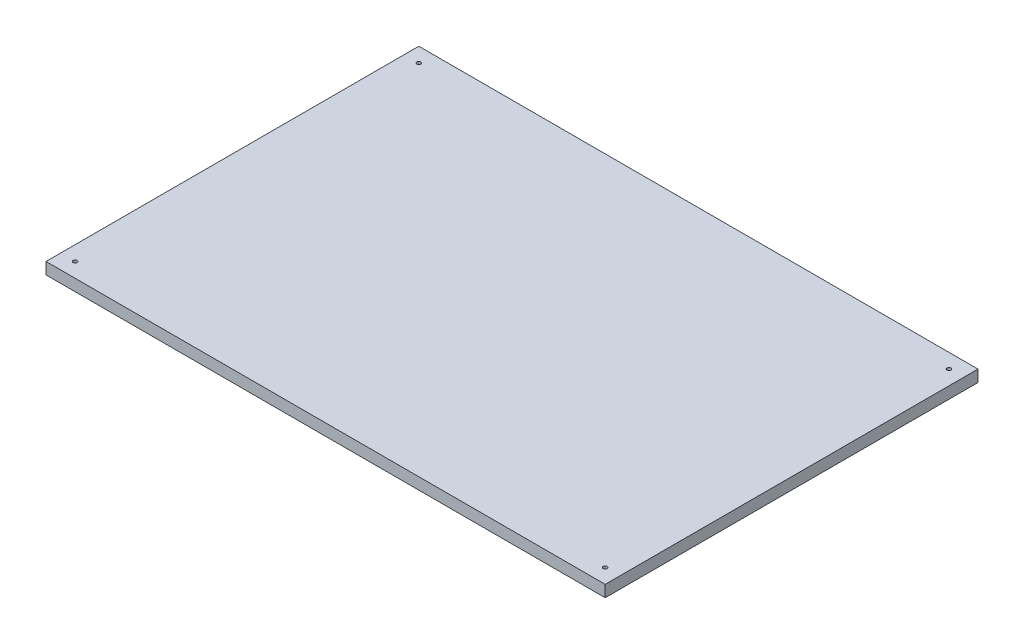
SolidWorks part; units mm, degrees
ref_plane "Front Plane" through (0, 0, 0) normal (0, 0, 1) x (1, 0, 0)
ref_plane "Top Plane" through (0, 0, 0) normal (0, 1, 0) x (1, 0, 0)
ref_plane "Right Plane" through (0, 0, 0) normal (1, 0, 0) x (0, 0, -1)
sketch "Sketch1" plane through (0, 0, 0) normal (0, 1, 0) x (1, 0, 0)
  line L1 (-239.5154, 77.7938) -> (240.4846, 77.7938)
  line L2 (-239.5154, 77.7938) -> (-239.5154, -242.2062)
  line L3 (-239.5154, -242.2062) -> (240.4846, -242.2062)
  line L4 (240.4846, 77.7938) -> (240.4846, -242.2062)
  dimension "D1" = 320
  dimension "D2" = 480
extrude "Boss-Extrude1" add sketch "Sketch1" along normal blind 10
sketch "Sketch2" plane through (0, 10, 0) normal (0, 1, 0) x (1, 0, 0)
  line L0 (-239.5154, 77.7938) -> (-239.5154, -242.2062) construction
  line L1 (240.4846, 77.7938) -> (-239.5154, 77.7938) construction
  line L2 (240.4846, -242.2062) -> (240.4846, 77.7938) construction
  line L3 (-239.5154, -242.2062) -> (240.4846, -242.2062) construction
  circle A0 centre (-227.0154, 65.2938) radius 1.7
  circle A1 centre (227.9846, -229.7062) radius 1.7
  circle A2 centre (227.9846, 65.2938) radius 1.7
  circle A3 centre (-227.0154, -229.7062) radius 1.7
  dimension "D1" = 12.5
  dimension "D2" = 12.5
  dimension "D3" = 12.5
  dimension "D4" = 12.5
  dimension "D5" = 12.5
  dimension "D6" = 12.5
  dimension "D7" = 12.5
  dimension "D8" = 12.5
extrude "Cut-Extrude1" cut sketch "Sketch2" against normal through all
